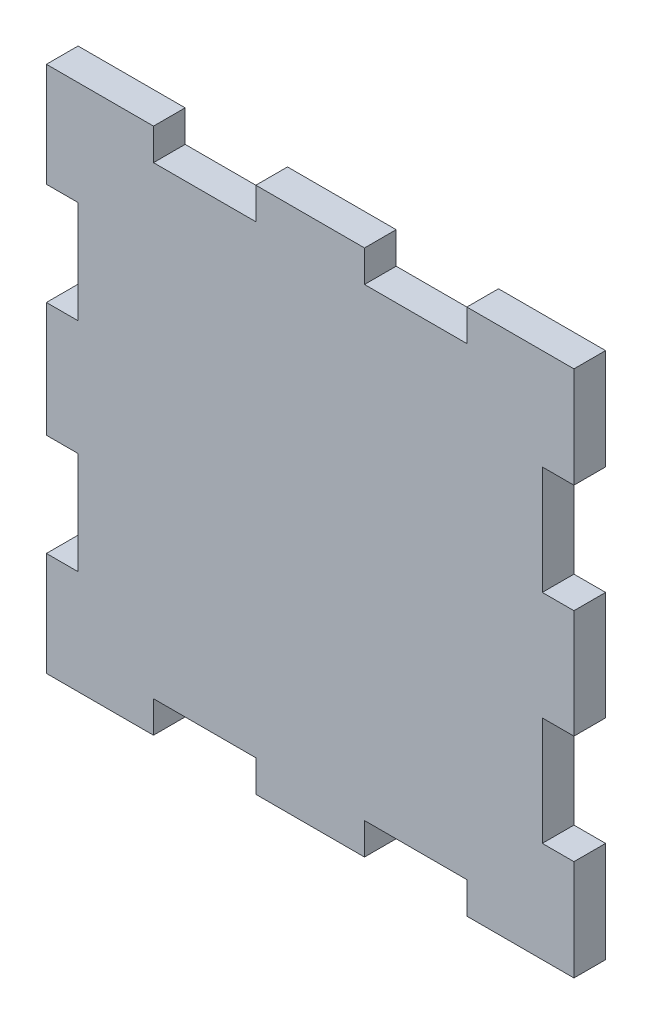
SolidWorks part; units mm, degrees
ref_plane "Alzado" through (0, 0, 0) normal (0, 0, 1) x (1, 0, 0)
ref_plane "Planta" through (0, 0, 0) normal (0, 1, 0) x (1, 0, 0)
ref_plane "Vista lateral" through (0, 0, 0) normal (1, 0, 0) x (0, 0, -1)
sketch "Croquis1" plane through (0, 0, 0) normal (0, 0, 1) x (1, 0, 0)
  line L0 (0, 20.8752) -> (0, -20.0871) construction
  line L1 (-25, -25) -> (-14.85, -25)
  line L2 (-25, -25) -> (-25, -15.15)
  line L3 (-25, 25) -> (-14.85, 25)
  line L4 (25, -25) -> (25, -15.45)
  line L5 (-25, -25) -> (25, 25) construction
  line L6 (-25, 25) -> (25, -25) construction
  line L7 (-23.5, 0) -> (26.5, 0) construction
  line L8 (25, 15.45) -> (22, 15.45)
  line L10 (25, 5.15) -> (22, 5.15)
  line L11 (22, 15.45) -> (22, 5.15)
  line L16 (25, -15.45) -> (22, -15.45)
  line L17 (22, -15.45) -> (22, -5.15)
  line L18 (25, -5.15) -> (22, -5.15)
  line L19 (25, -5.15) -> (25, 5.15)
  line L20 (25, 15.45) -> (25, 25)
  line L21 (22, 5.15) -> (22, 10.3) construction
  line L22 (-25, 15.15) -> (-22, 15.15)
  line L24 (-25, 5.45) -> (-22, 5.45)
  line L25 (-22, 15.15) -> (-22, 5.45)
  line L26 (-22, 5.45) -> (-22, 10.3) construction
  line L27 (22, 10.3) -> (-22, 10.3) construction
  line L28 (-25, 15.15) -> (-25, 25)
  line L29 (-25, -5.45) -> (-22, -5.45)
  line L30 (-22, -15.15) -> (-22, -5.45)
  line L31 (-25, -15.15) -> (-22, -15.15)
  line L32 (-25, -5.45) -> (-25, 5.45)
  line L33 (-5.15, -25) -> (5.15, -25)
  line L35 (-14.85, -25) -> (-14.85, -22)
  line L36 (-14.85, -22) -> (-5.15, -22)
  line L37 (-5.15, -25) -> (-5.15, -22)
  line L38 (5.15, -25) -> (5.15, -22)
  line L39 (14.85, -22) -> (5.15, -22)
  line L40 (14.85, -25) -> (14.85, -22)
  line L41 (14.85, -25) -> (25, -25)
  line L42 (14.85, 25) -> (14.85, 22)
  line L43 (14.85, 22) -> (5.15, 22)
  line L44 (5.15, 25) -> (5.15, 22)
  line L45 (-5.15, 25) -> (-5.15, 22)
  line L46 (-14.85, 22) -> (-5.15, 22)
  line L47 (-14.85, 25) -> (-14.85, 22)
  line L48 (-5.15, 25) -> (5.15, 25)
  line L49 (14.85, 25) -> (25, 25)
  point P0 (0, 0)
  point P46 (25, 0)
  dimension "D5" = 9.7
  dimension "D6" = 3
  dimension "D7" = 3
  dimension "D8" = 9.7
  dimension "D9" = 5.15
  dimension "D3" = 3
  dimension "D2" = 50
  dimension "D10" = 50
  dimension "D4" = 5.15
extrude "Saliente-Extruir1" add sketch "Croquis1" along normal blind 3
equation "\"A\"= 3"
equation "\"B\"= 50"
equation "\"C\"= 10"
equation "\"D\"= 10"
equation "\"D5@Croquis1\"=\"C\"-.3"
equation "\"D6@Croquis1\"=\"A\""
equation "\"D7@Croquis1\"=\"A\""
equation "\"D8@Croquis1\"=\"C\"-.3"
equation "\"D9@Croquis1\"=(\"D\"+.3)/2"
equation "\"D3@Croquis1\"=\"A\""
equation "\"D2@Croquis1\"=\"B\""
equation "\"D10@Croquis1\"=\"B\""
equation "\"D4@Croquis1\"=(\"D\"+.3)/2"
